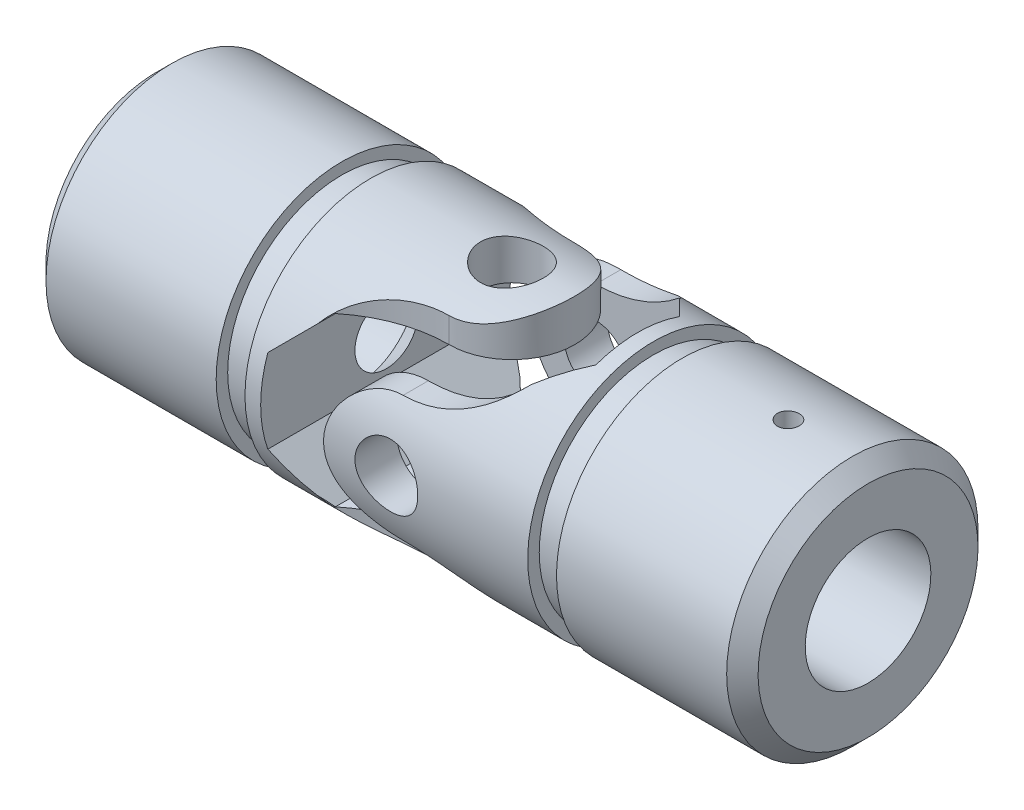
SolidWorks part; units mm, degrees
ref_plane "Front Plane" through (0, 0, 0) normal (0, 0, 1) x (1, 0, 0)
ref_plane "Top Plane" through (0, 0, 0) normal (0, 1, 0) x (1, 0, 0)
ref_plane "Right Plane" through (0, 0, 0) normal (1, 0, 0) x (0, 0, -1)
sketch "Sketch0" plane through (0, 0, 0) normal (0, 1, 0) x (1, 0, 0)
  line L0 (-53.975, 0) -> (53.975, 0) construction
  line L1 (-53.975, 19.05) -> (-53.975, -19.05) construction
  line L2 (-23.8125, 9.525) -> (-23.8125, -9.525) construction
  line L3 (-23.8125, 9.525) -> (-14.2875, 0) construction
  line L4 (-14.2875, 0) -> (-23.8125, -9.525) construction
  line L5 (-19.05, 4.7625) -> (-19.05, -4.7625) construction
  point P7 (-23.8125, 0)
  point P8 (0, 0)
  point P12 (-19.05, 0)
sketch "Sketch1" plane through (0, 0, 0) normal (0, 1, 0) x (1, 0, 0)
  line L0 (-53.975, 19.05) -> (-25.7969, 19.05)
  line L1 (9.525, 19.05) -> (9.525, 0)
  line L2 (9.525, 0) -> (-53.975, 0)
  line L3 (-53.975, 0) -> (-53.975, 19.05)
  line L4 (-53.975, 19.05) -> (-53.975, -19.05) construction
  line L5 (-53.975, 0) -> (53.975, 0) construction
  line L6 (-21.4312, 19.05) -> (9.525, 19.05)
  line L7 (-21.4312, 4.7625) -> (-21.4312, 17.3038) construction
  line L8 (-25.7969, 19.05) -> (-25.7969, 17.3038)
  line L9 (-25.7969, 17.3038) -> (-21.4312, 17.3038)
  line L10 (-21.4312, 19.05) -> (-21.4312, 17.3038)
  line L11 (0, 0) -> (19.05, 0) construction
  line L12 (-19.05, 4.7625) -> (-23.8125, 4.7625) construction
  line L13 (-23.8125, 9.525) -> (-23.8125, -9.525) construction
  circle A0 centre (0, 0) radius 19.05 construction
  dimension "D1" = 4.3656
  dimension "D2" = 1.7462
  dimension "D3" = 63.5
revolve "Revolve1" add sketch "Sketch1" angle 360 about L0
chamfer "Chamfer1" distance 2.3813 angle 45 1 edges at (-53.975, 0, 19.05)
sketch "Sketch2" plane through (0, 0, 0) normal (0, 1, 0) x (1, 0, 0)
  line L0 (-21.4312, 19.05) -> (-17.0656, 19.05) construction
  line L1 (-21.4312, 19.05) -> (9.525, 19.05) construction
  line L2 (9.525, 19.05) -> (-21.4312, 19.05) construction
  line L3 (-25.7969, 17.3038) -> (-21.4312, 17.3038) construction
  line L4 (-53.975, 0) -> (9.525, 0) construction
  line L5 (-17.0656, 19.05) -> (19.05, 19.05)
  line L6 (19.05, 19.05) -> (19.05, -19.05)
  line L7 (19.05, -19.05) -> (-17.0656, -19.05)
  line L8 (0, 9.525) -> (0, 0) construction
  arc A0 (-17.0656, 19.05) -> (0, 9.525) centre (0, 29.5755) ccw
  arc A1 (0, -9.525) -> (0, 9.525) centre (0, 0) ccw
  arc A2 (-17.0656, -19.05) -> (0, -9.525) centre (0, -29.5755) cw
  dimension "D1" = 19.05
extrude "Extrude1" cut sketch "Sketch2" against normal through all and the other way through all
sketch "Sketch3" plane through (0, 0, 0) normal (0, 0, 1) x (1, 0, 0)
  line L0 (-12.7063, 12.6873) -> (-19.05, 6.3437)
  line L1 (-12.7063, 12.6873) -> (19.05, 12.6873)
  line L2 (-19.05, 6.3437) -> (-19.05, -6.3437)
  line L3 (-12.7063, -12.6873) -> (19.05, -12.6873)
  line L4 (19.05, 12.6873) -> (19.05, -12.6873)
  line L5 (-19.05, -6.3437) -> (-12.7063, -12.6873)
  dimension "D1" = 25.3746
  dimension "D2" = 6.3437
extrude "Extrude3" cut sketch "Sketch3" against normal through all and the other way through all
sketch "Sketch4" plane through (-53.975, 0, 0) normal (-1, 0, 0) x (0, 0, 1)
  circle A0 centre (0, 0) radius 9.525
extrude "Extrude4" cut sketch "Sketch4" against normal up to vertex (30.1625 mm away) up to point (-23.8125, 0, -9.525)
sketch "Sketch5" plane through (-23.8125, 0, 0) normal (-1, 0, 0) x (0, 0, 1)
  circle A0 centre (0, 0) radius 9.525 construction
  circle A1 centre (0, 0) radius 9.525
extrude "Extrude5" cut sketch "Sketch5" against normal through all draft 45
sketch "Sketch6" plane through (0, 0, 0) normal (0, 1, 0) x (1, 0, 0)
  line L0 (-53.975, 0) -> (53.975, 0) construction
  line L1 (9.525, 0) -> (4.7625, 0) construction
  line L2 (4.7625, 0) -> (0, 0) construction
  circle A0 centre (0, 0) radius 4.7625
  arc A1 (0, -9.525) -> (0, 9.525) centre (0, 0) ccw construction
  dimension "D1" = 9.525
extrude "Extrude6" cut sketch "Sketch6" against normal through all and the other way through all
sketch "Sketch22" plane through (0, 0, 0) normal (1, 0, 0) x (0, 0, -1)
  circle A0 centre (0, 0) radius 9.525
mirror "Mirror1" about plane through (0, 0, 0) normal (1, 0, 0) of bodies 109 122
move or copy body "Body-Move/Copy1" bodies to move or copy 110 copy no rotation origin (0, 0, 0) rotation axis (1, 0, 0) rotation angle 90
sketch "Sketch18" plane through (0, 0, 0) normal (0, 1, 0) x (1, 0, 0)
  line L0 (-53.975, -9.525) -> (-23.8125, -9.525)
  line L3 (-53.975, 9.525) -> (-23.8125, 9.525)
  line L4 (-23.8125, 9.525) -> (-23.8125, -9.525)
  line L9 (53.975, -16.6687) -> (53.975, 16.6687) construction
  line L10 (-53.975, 16.6687) -> (-53.975, -16.6687) construction
  line L11 (-23.8125, -9.525) -> (-23.8125, 9.525) construction
  line L12 (53.975, 0) -> (53.975, 19.05) construction
  line L14 (131.7625, 9.525) -> (131.7625, -9.525)
  line L15 (161.925, 9.525) -> (131.7625, 9.525)
  line L16 (161.925, -9.525) -> (131.7625, -9.525)
sketch "Sketch19" plane through (0, 0, 0) normal (0, 1, 0) x (1, 0, 0)
  line L0 (23.8125, 0) -> (53.975, 0) construction
  line L1 (53.975, -16.6687) -> (53.975, 16.6687) construction
  line L2 (23.8125, -9.525) -> (23.8125, 9.525) construction
  circle A0 centre (41.91, 0) radius 1.651
  dimension "hole" = 3.302
  dimension "D1" = 30.1625
  dimension "D2" = 12.065
extrude "Cut-Extrude1" cut sketch "Sketch19" against normal through all and the other way through all
ref_plane "Plane1" through (41.91, 0, 0) normal (1, 0, 0) x (0, 0, -1)
move or copy body "Body-Move/Copy2" [suppressed] bodies to move or copy 140 copy no rotation origin (0, 0, 0) rotation axis (0, 0, -1) rotation angle 25
ref_plane "Plane2" through (0, 0, 0) normal (0, 1, 0) x (1, 0, 0)
ref_point "Point1"
ref_point "Point2"
ref_plane "Plane3" through (-23.8125, 0, 0) normal (1, 0, 0) x (0, 0, -1)
ref_point "Point3"
ref_point "Point4"
equation "\"D1@Sketch3\" = \"OD@Sketch0\"*.666"
equation "\"D2@Sketch3\" = \"D1@Sketch3\"/4"
equation "\"D1@Chamfer1\"= \"OD@Sketch0\" / 16"
